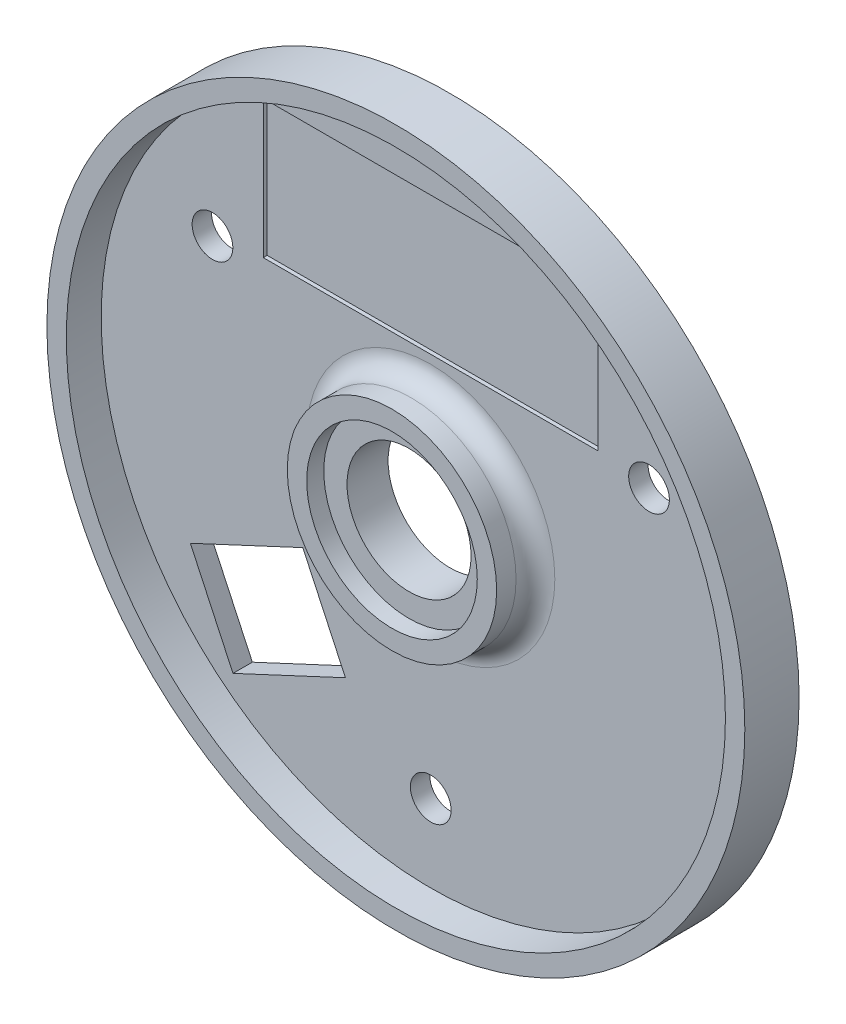
SolidWorks part; units mm, degrees
other "Markup1"
sketch "Sketch12" plane through (50, -50, 11.5) normal (0.8404, -0.0169, 0.5417) x (0.5411, -0.0298, -0.8404)
ref_plane "Front Plane" through (0, 0, 0) normal (0, 0, 1) x (1, 0, 0)
ref_plane "Top Plane" through (0, 0, 0) normal (0, 1, 0) x (1, 0, 0)
ref_plane "Right Plane" through (0, 0, 0) normal (1, 0, 0) x (0, 0, -1)
sketch "Sketch1" plane through (0, 0, 0) normal (0, 0, 1) x (1, 0, 0)
  circle A0 centre (0, 0) radius 45
  dimension "D1" = 90
extrude "Boss-Extrude1" add sketch "Sketch1" along normal blind 2.5 contours A0
sketch "Sketch2" plane through (0, 0, 2.5) normal (0, 0, 1) x (1, 0, 0)
  circle A0 centre (0, 0) radius 45
  circle A1 centre (0, 0) radius 42.5
  dimension "D1" = 90
  dimension "D2" = 85
extrude "Boss-Extrude2" add sketch "Sketch2" along normal blind 4.5 contours A0 | A1
sketch "Sketch3" plane through (0, 0, 2.5) normal (0, 0, 1) x (1, 0, 0)
  circle A0 centre (0, 0) radius 8
  dimension "D1" = 16
extrude "Cut-Extrude1" cut sketch "Sketch3" against normal blind 10
sketch "Sketch5" plane through (0, 0, 2.5) normal (0, 0, 1) x (1, 0, 0)
  circle A0 centre (0, 0) radius 13.5
  circle A1 centre (0, 0) radius 11
  dimension "D1" = 27
  dimension "D2" = 22
extrude "Boss-Extrude3" add sketch "Sketch5" along normal blind 5
sketch "Sketch7" plane through (0, 0, 2.5) normal (0, 0, 1) x (1, 0, 0)
  line L1 (21.59, 17.11) -> (-21.59, 17.11)
  line L2 (21.59, 17.11) -> (21.59, 34.89)
  line L3 (21.59, 34.89) -> (-21.59, 34.89)
  line L4 (-21.59, 17.11) -> (-21.59, 34.89)
  line L5 (21.59, 17.11) -> (-21.59, 34.89) construction
  line L6 (21.59, 34.89) -> (-21.59, 17.11) construction
  point P0 (0, 26)
  dimension "D1" = 43.18
  dimension "D2" = 17.78
  dimension "D3" = 26
extrude "Cut-Extrude2" cut sketch "Sketch7" against normal blind 0.5
sketch "Sketch8" plane through (0, 0, 2.5) normal (0, 0, 1) x (1, 0, 0)
  line L0 (-65, 0) -> (65, 0) construction
  line L1 (-16.4966, -12.7281) -> (-11.0025, -24.5101)
  line L2 (-16.4966, -12.7281) -> (-30.9975, -19.4899)
  line L3 (-30.9975, -19.4899) -> (-25.5034, -31.2719)
  line L4 (-11.0025, -24.5101) -> (-25.5034, -31.2719)
  line L5 (-16.4966, -12.7281) -> (-25.5034, -31.2719) construction
  line L6 (-30.9975, -19.4899) -> (-11.0025, -24.5101) construction
  point P0 (-21, -22)
  dimension "D1" = 13
  dimension "D2" = 16
  dimension "D3" = 22
  dimension "D4" = 25
  dimension "D5" = 65
  dimension "D6" = 130
  dimension "D7" = 21
extrude "Cut-Extrude3" cut sketch "Sketch8" against normal blind 5
sketch "Sketch9" plane through (0, 0, 0) normal (0, 0, -1) x (-1, 0, 0)
  line L0 (25.5034, -31.2719) -> (11.0025, -24.5101) construction
  line L1 (27.2501, -13.329) -> (27.884, -11.9695)
  line L2 (27.2501, -13.329) -> (29.2893, -14.2799)
  line L3 (32.688, -15.8647) -> (33.3219, -14.5053)
  line L4 (27.884, -11.9695) -> (29.9232, -12.9204)
  line L5 (30.6488, -14.9138) -> (32.688, -15.8647)
  line L6 (29.9232, -12.9204) -> (30.8741, -10.8812)
  line L7 (28.3384, -16.3191) -> (29.2893, -14.2799)
  line L8 (28.3384, -16.3191) -> (29.6979, -16.953)
  line L9 (29.6979, -16.953) -> (30.6488, -14.9138)
  line L10 (30.8741, -10.8812) -> (32.2336, -11.5152)
  line L11 (31.2827, -13.5544) -> (33.3219, -14.5053)
  line L12 (31.2827, -13.5544) -> (32.2336, -11.5152)
  line L20 (18.187, -9.1028) -> (18.821, -7.7434)
  line L21 (18.187, -9.1028) -> (23.6249, -11.6385)
  line L22 (23.6249, -11.6385) -> (24.2588, -10.2791)
  line L23 (18.821, -7.7434) -> (24.2588, -10.2791)
  line L24 (11.0025, -24.5101) -> (16.4966, -12.7281) construction
  line L25 (16.4966, -12.7281) -> (30.9975, -19.4899) construction
  line L26 (30.9975, -19.4899) -> (25.5034, -31.2719) construction
  dimension "D1" = 6
  dimension "D2" = 6
  dimension "D3" = 1.5
  dimension "D4" = 1.5
  dimension "D5" = 4
  dimension "D6" = 1.5
  dimension "D7" = 6
  dimension "D8" = 4
  dimension "D9" = 2.25
  dimension "D10" = 2.25
extrude "Cut-Extrude4" cut sketch "Sketch9" against normal blind 0.5 contours L4 L6 L10 L12 L11 L3 L5 L9 L8 L7 L2 L1 | L23 L22 L21 L20
sketch "Sketch11" plane through (0, 0, 2.5) normal (0, 0, 1) x (1, 0, 0)
  circle A0 centre (0, 0) radius 13.5
  circle A1 centre (0, 0) radius 8
  dimension "D1" = 27
  dimension "D2" = 16
extrude "Boss-Extrude4" add sketch "Sketch11" along normal blind 2.8
sketch "Sketch14" plane through (0, 0, 2.5) normal (0, 0, 1) x (1, 0, 0)
  circle A4 centre (0, 0) radius 32.5
  circle A5 centre (0, -32.5) radius 2.625
  circle A6 centre (-28.1458, 16.25) radius 2.625
  circle A7 centre (28.1458, 16.25) radius 2.625
  point P11 (0, 0)
  point P13 (0, 0)
  dimension "D1" = 65
  dimension "D2" = 5.25
  dimension "D3" = 3
extrude "Cut-Extrude5" cut sketch "Sketch14" against normal through all both and the other way through all
fillet "Fillet1" radius 2.5 1 edges at (13.5, 0, 2.5)
